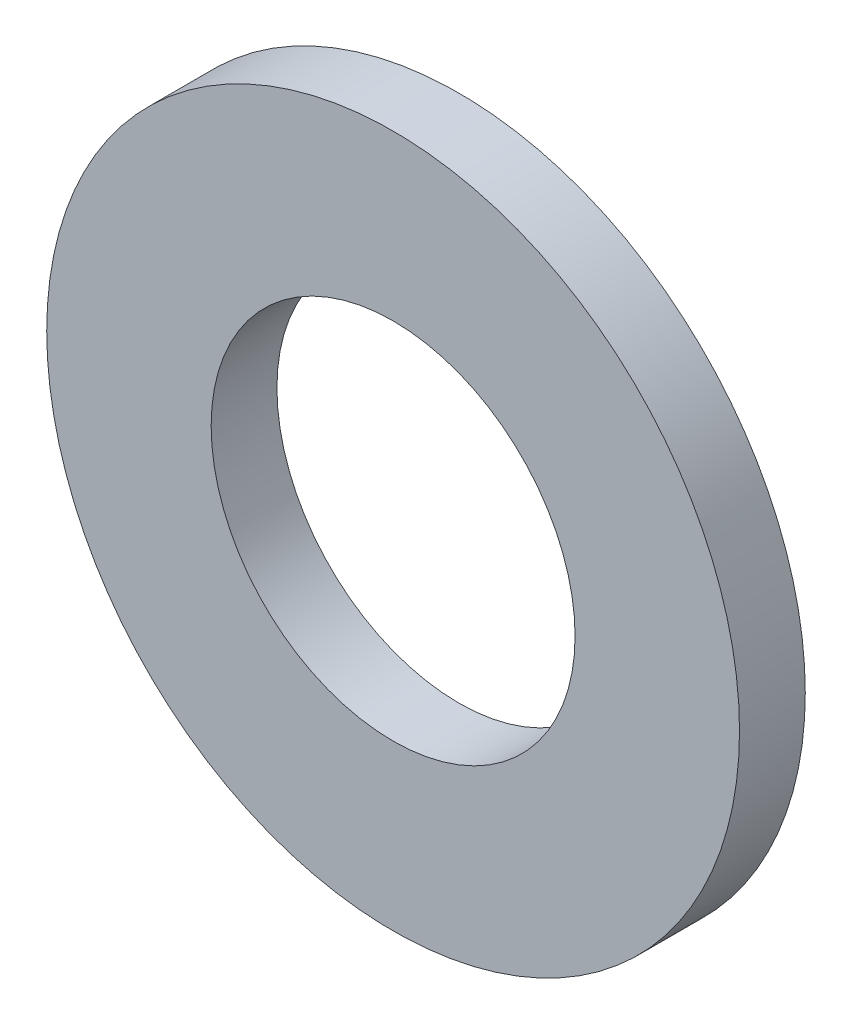
SolidWorks part; units mm, degrees
ref_plane "Спереди" through (0, 0, 0) normal (0, 0, 1) x (1, 0, 0)
ref_plane "Сверху" through (0, 0, 0) normal (0, 1, 0) x (1, 0, 0)
ref_plane "Справа" through (0, 0, 0) normal (1, 0, 0) x (0, 0, -1)
sketch "Sketch2" plane through (0, 0, 0) normal (0, 0, 1) x (1, 0, 0)
  circle A0 centre (0, 0) radius 4.15
  circle A1 centre (0, 0) radius 7.9
  dimension "D1" = 15.8
  dimension "D2" = 8.3
extrude "Boss-Extrude1" add sketch "Sketch2" along normal blind 1.5
